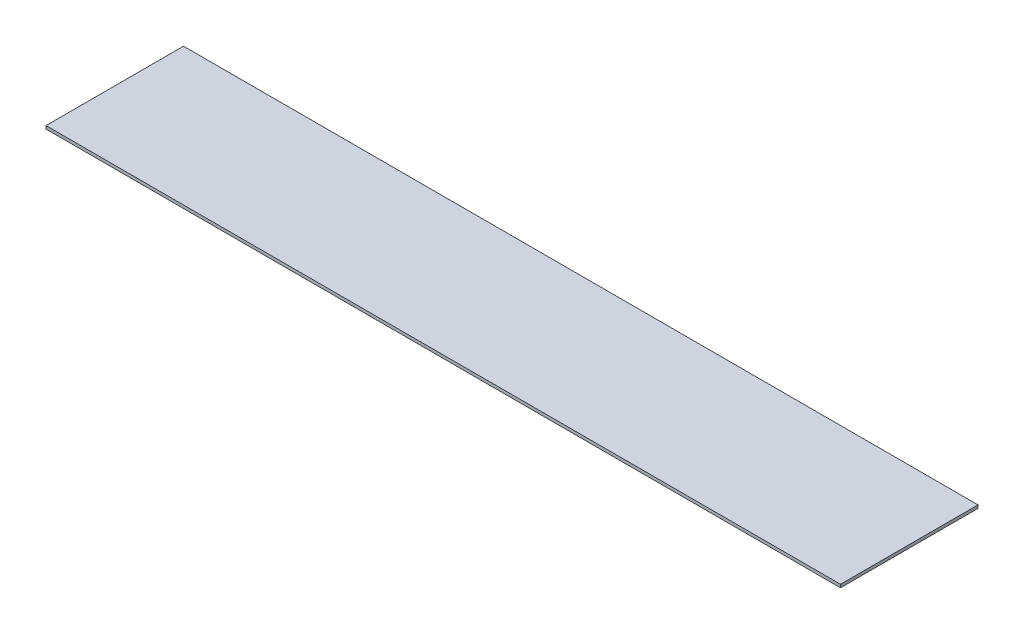
SolidWorks part; units mm, degrees
ref_plane "Front Plane" through (0, 0, 0) normal (0, 0, 1) x (1, 0, 0)
ref_plane "Top Plane" through (0, 0, 0) normal (0, 1, 0) x (1, 0, 0)
ref_plane "Right Plane" through (0, 0, 0) normal (1, 0, 0) x (0, 0, -1)
sketch "Sketch1" plane through (0, 0, 0) normal (0, 1, 0) x (1, 0, 0)
  line L1 (-151.4961, 99.7008) -> (108.5039, 99.7008)
  line L2 (-151.4961, 99.7008) -> (-151.4961, 54.7008)
  line L3 (-151.4961, 54.7008) -> (108.5039, 54.7008)
  line L4 (108.5039, 99.7008) -> (108.5039, 54.7008)
  dimension "D1" = 260
  dimension "D2" = 45
extrude "Boss-Extrude1" add sketch "Sketch1" along normal blind 1
